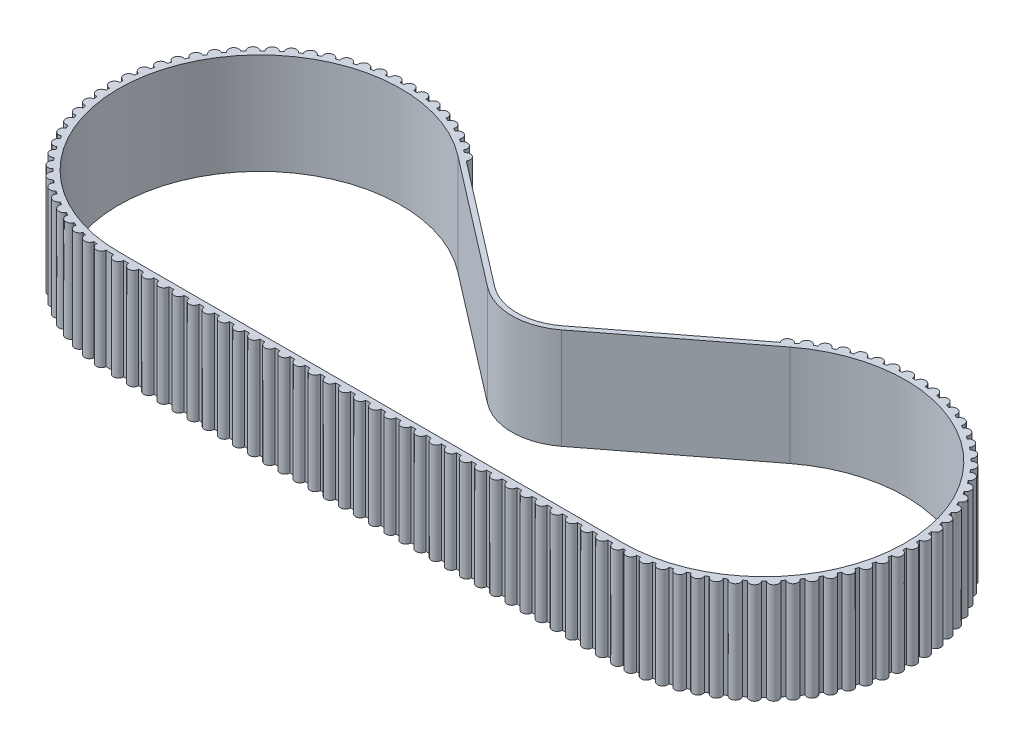
SolidWorks part; units mm, degrees
ref_plane "Front Plane" through (0, 0, 0) normal (0, 0, 1) x (1, 0, 0)
ref_plane "Top Plane" through (0, 0, 0) normal (0, 1, 0) x (1, 0, 0)
ref_plane "Right Plane" through (0, 0, 0) normal (1, 0, 0) x (0, 0, -1)
sketch "Sketch1" plane through (0, 0, 0) normal (0, 1, 0) x (1, 0, 0)
  line L0 (0, 0) -> (50, 0) construction
  line L1 (0, 14) -> (50, 14) construction
  line L2 (0, -14) -> (50, -14) construction
  line L3 (0, 14) -> (25, 6) construction
  line L4 (25, 6) -> (50, 14) construction
  line L5 (25, 6) -> (25, 14) construction
  line L6 (28.6587, 1.2446) -> (41.463, 11.096)
  line L7 (21.3413, 1.2446) -> (8.537, 11.096)
  circle A0 centre (0, 0) radius 14 construction
  circle A1 centre (50, 0) radius 14 construction
  circle A2 centre (25, 6) radius 6 construction
  arc A3 (8.537, 11.096) -> (0, -14) centre (0, 0) ccw
  arc A4 (41.463, 11.096) -> (50, -14) centre (50, 0) cw
  arc A5 (21.3413, 1.2446) -> (28.6587, 1.2446) centre (25, 6) ccw
  dimension "D1" = 28
  dimension "D2" = 12
  dimension "D3" = 50
  dimension "D4" = 8
sketch "Sketch2" plane through (0, 0, 0) normal (0, 1, 0) x (1, 0, 0)
  line L0 (1, -14.5) -> (1.5, -14.5)
  line L1 (49, -14.5) -> (49.5, -14.5)
  line L2 (28.6587, 1.2446) -> (41.463, 11.096)
  line L3 (21.3413, 1.2446) -> (8.537, 11.096)
  line L4 (47.5, -14.5) -> (48, -14.5)
  line L5 (21.6462, 1.6409) -> (8.8419, 11.4922) construction
  line L6 (28.3538, 1.6409) -> (41.1581, 11.4922) construction
  line L7 (46, -14.5) -> (46.5, -14.5)
  line L8 (44.5, -14.5) -> (45, -14.5)
  line L9 (43, -14.5) -> (43.5, -14.5)
  line L10 (41.5, -14.5) -> (42, -14.5)
  line L11 (40, -14.5) -> (40.5, -14.5)
  line L12 (38.5, -14.5) -> (39, -14.5)
  line L13 (37, -14.5) -> (37.5, -14.5)
  line L14 (35.5, -14.5) -> (36, -14.5)
  line L15 (34, -14.5) -> (34.5, -14.5)
  line L16 (32.5, -14.5) -> (33, -14.5)
  line L17 (31, -14.5) -> (31.5, -14.5)
  line L18 (29.5, -14.5) -> (30, -14.5)
  line L19 (28, -14.5) -> (28.5, -14.5)
  line L20 (26.5, -14.5) -> (27, -14.5)
  line L21 (25, -14.5) -> (25.5, -14.5)
  line L22 (23.5, -14.5) -> (24, -14.5)
  line L23 (22, -14.5) -> (22.5, -14.5)
  line L24 (20.5, -14.5) -> (21, -14.5)
  line L25 (19, -14.5) -> (19.5, -14.5)
  line L26 (17.5, -14.5) -> (18, -14.5)
  line L27 (16, -14.5) -> (16.5, -14.5)
  line L28 (14.5, -14.5) -> (15, -14.5)
  line L29 (13, -14.5) -> (13.5, -14.5)
  line L30 (11.5, -14.5) -> (12, -14.5)
  line L31 (10, -14.5) -> (10.5, -14.5)
  line L32 (8.5, -14.5) -> (9, -14.5)
  line L33 (7, -14.5) -> (7.5, -14.5)
  line L34 (5.5, -14.5) -> (6, -14.5)
  line L35 (4, -14.5) -> (4.5, -14.5)
  line L36 (2.5, -14.5) -> (3, -14.5)
  line L37 (25, 6) -> (25, 14) construction
  line L38 (0, 14) -> (50, 14) construction
  line L39 (9.4327, 11.0377) -> (21.6462, 1.6409)
  line L40 (40.5792, 11.0227) -> (28.3538, 1.6409)
  line L41 (0, -14) -> (50, -14)
  line L45 (0, -14) -> (50, -14) construction
  line L47 (0, -14.5) -> (50, -14.5) construction
  arc A0 (0, -14.5) -> (1, -14.5) centre (0.5, -14.5) ccw
  arc A1 (0, -14) -> (8.537, 11.096) centre (0, 0) cw
  arc A2 (8.537, 11.096) -> (0, -14) centre (0, 0) ccw construction
  arc A3 (21.3413, 1.2446) -> (28.6587, 1.2446) centre (25, 6) ccw
  arc A4 (21.3413, 1.2446) -> (28.6587, 1.2446) centre (25, 6) ccw construction
  arc A5 (41.463, 11.096) -> (50, -14) centre (50, 0) cw
  arc A6 (50, -14) -> (41.463, 11.096) centre (50, 0) ccw construction
  arc A7 (0, -14.5) -> (8.8419, 11.4922) centre (0, 0) cw construction
  arc A8 (21.6462, 1.6409) -> (28.3538, 1.6409) centre (25, 6) ccw
  arc A9 (41.3612, 11.6457) -> (41.6459, 11.8515) centre (50, 0) cw
  arc A10 (1.5, -14.5) -> (2.5, -14.5) centre (2, -14.5) ccw
  arc A11 (3, -14.5) -> (4, -14.5) centre (3.5, -14.5) ccw
  arc A12 (4.5, -14.5) -> (5.5, -14.5) centre (5, -14.5) ccw
  arc A13 (6, -14.5) -> (7, -14.5) centre (6.5, -14.5) ccw
  arc A14 (7.5, -14.5) -> (8.5, -14.5) centre (8, -14.5) ccw
  arc A15 (9, -14.5) -> (10, -14.5) centre (9.5, -14.5) ccw
  arc A16 (10.5, -14.5) -> (11.5, -14.5) centre (11, -14.5) ccw
  arc A17 (12, -14.5) -> (13, -14.5) centre (12.5, -14.5) ccw
  arc A18 (13.5, -14.5) -> (14.5, -14.5) centre (14, -14.5) ccw
  arc A19 (15, -14.5) -> (16, -14.5) centre (15.5, -14.5) ccw
  arc A20 (16.5, -14.5) -> (17.5, -14.5) centre (17, -14.5) ccw
  arc A21 (18, -14.5) -> (19, -14.5) centre (18.5, -14.5) ccw
  arc A22 (19.5, -14.5) -> (20.5, -14.5) centre (20, -14.5) ccw
  arc A23 (21, -14.5) -> (22, -14.5) centre (21.5, -14.5) ccw
  arc A24 (22.5, -14.5) -> (23.5, -14.5) centre (23, -14.5) ccw
  arc A25 (24, -14.5) -> (25, -14.5) centre (24.5, -14.5) ccw
  arc A26 (25.5, -14.5) -> (26.5, -14.5) centre (26, -14.5) ccw
  arc A27 (27, -14.5) -> (28, -14.5) centre (27.5, -14.5) ccw
  arc A28 (28.5, -14.5) -> (29.5, -14.5) centre (29, -14.5) ccw
  arc A29 (30, -14.5) -> (31, -14.5) centre (30.5, -14.5) ccw
  arc A30 (31.5, -14.5) -> (32.5, -14.5) centre (32, -14.5) ccw
  arc A31 (33, -14.5) -> (34, -14.5) centre (33.5, -14.5) ccw
  arc A32 (34.5, -14.5) -> (35.5, -14.5) centre (35, -14.5) ccw
  arc A33 (36, -14.5) -> (37, -14.5) centre (36.5, -14.5) ccw
  arc A34 (37.5, -14.5) -> (38.5, -14.5) centre (38, -14.5) ccw
  arc A35 (39, -14.5) -> (40, -14.5) centre (39.5, -14.5) ccw
  arc A36 (40.5, -14.5) -> (41.5, -14.5) centre (41, -14.5) ccw
  arc A37 (42, -14.5) -> (43, -14.5) centre (42.5, -14.5) ccw
  arc A38 (43.5, -14.5) -> (44.5, -14.5) centre (44, -14.5) ccw
  arc A39 (45, -14.5) -> (46, -14.5) centre (45.5, -14.5) ccw
  arc A40 (46.5, -14.5) -> (47.5, -14.5) centre (47, -14.5) ccw
  arc A41 (48, -14.5) -> (49, -14.5) centre (48.5, -14.5) ccw
  arc A42 (49.5, -14.5) -> (50.4999, -14.4914) centre (50, -14.5) ccw
  arc A43 (50.753, -14.4804) -> (51.7491, -14.3941) centre (51.2518, -14.4459) ccw
  arc A44 (52.0973, -14.3475) -> (53.081, -14.1689) centre (52.5907, -14.2667) ccw
  arc A45 (53.4234, -14.0901) -> (54.3862, -13.8207) centre (53.9071, -13.9637) ccw
  arc A46 (54.7198, -13.7104) -> (55.6534, -13.3525) centre (55.1897, -13.5395) ccw
  arc A47 (55.9752, -13.2116) -> (56.8715, -12.7684) centre (56.4271, -12.9978) ccw
  arc A48 (57.1788, -12.5982) -> (58.0299, -12.0736) centre (57.6089, -12.3432) ccw
  arc A49 (58.32, -11.8755) -> (59.1186, -11.2739) centre (58.7245, -11.5816) ccw
  arc A50 (59.3891, -11.0497) -> (60.1282, -10.3764) centre (59.7645, -10.7194) ccw
  arc A51 (60.3766, -10.128) -> (61.0499, -9.3888) centre (60.7197, -9.7642) ccw
  arc A52 (61.2741, -9.1183) -> (61.8757, -8.3197) centre (61.5818, -8.7242) ccw
  arc A53 (62.0738, -8.0296) -> (62.5984, -7.1784) centre (62.3434, -7.6085) ccw
  arc A54 (62.7686, -6.8711) -> (63.2118, -5.9748) centre (62.9979, -6.4268) ccw
  arc A55 (63.3527, -5.653) -> (63.7105, -4.7194) centre (63.5396, -5.1893) ccw
  arc A56 (63.8208, -4.3859) -> (64.0902, -3.423) centre (63.9638, -3.9067) ccw
  arc A57 (64.169, -3.0806) -> (64.3476, -2.0969) centre (64.2668, -2.5903) ccw
  arc A58 (64.3942, -1.7487) -> (64.4805, -0.7526) centre (64.4459, -1.2514) ccw
  arc A59 (64.4944, -0.4015) -> (64.4877, 0.5983) centre (64.4997, 0.0984) ccw
  arc A60 (64.4689, 0.9491) -> (64.3691, 1.9439) centre (64.4276, 1.4474) ccw
  arc A61 (64.3178, 2.2915) -> (64.1258, 3.2727) centre (64.2303, 2.7838) ccw
  arc A62 (64.0424, 3.614) -> (63.76, 4.5731) centre (63.9095, 4.096) ccw
  arc A63 (63.6451, 4.9051) -> (63.2747, 5.8338) centre (63.4679, 5.3726) ccw
  arc A64 (63.1295, 6.1537) -> (62.6742, 7.0438) centre (62.9095, 6.6027) ccw
  arc A65 (62.4998, 7.3488) -> (61.9636, 8.1927) centre (62.239, 7.7754) ccw
  arc A66 (61.7617, 8.4802) -> (61.1493, 9.2706) centre (61.4623, 8.8806) ccw
  arc A67 (60.9214, 9.5379) -> (60.2382, 10.2679) centre (60.5861, 9.9088) ccw
  arc A68 (59.9864, 10.5129) -> (59.2382, 11.1761) centre (59.618, 10.851) ccw
  arc A69 (58.9647, 11.3966) -> (58.158, 11.9873) centre (58.5665, 11.699) ccw
  arc A70 (57.8652, 12.1815) -> (57.0071, 12.6945) centre (57.4406, 12.4454) ccw
  arc A71 (56.6975, 12.8606) -> (55.7953, 13.2915) centre (56.2501, 13.0838) ccw
  arc A72 (55.4716, 13.428) -> (54.5332, 13.7732) centre (55.0054, 13.6087) ccw
  arc A73 (54.1982, 13.8789) -> (53.2318, 14.1353) centre (53.7172, 14.0154) ccw
  arc A74 (52.8884, 14.2094) -> (51.9023, 14.3747) centre (52.3968, 14.3005) ccw
  arc A75 (51.5535, 14.4165) -> (50.5563, 14.4893) centre (51.0555, 14.4615) ccw
  arc A76 (50.2051, 14.4985) -> (49.2055, 14.4782) centre (49.7051, 14.497) ccw
  arc A77 (48.855, 14.4547) -> (47.8615, 14.3414) centre (48.3573, 14.4066) ccw
  arc A78 (47.5147, 14.2854) -> (46.5362, 14.0802) centre (47.0237, 14.1913) ccw
  arc A79 (46.1961, 13.9922) -> (45.2409, 13.6967) centre (45.7159, 13.8527) ccw
  arc A80 (44.9105, 13.5774) -> (43.9869, 13.1944) centre (44.4454, 13.3939) ccw
  arc A81 (43.669, 13.0449) -> (42.7851, 12.5776) centre (43.223, 12.8188) ccw
  arc A82 (42.4825, 12.3991) -> (41.6459, 11.8515) centre (42.0595, 12.1325) ccw
  arc A83 (41.3612, 11.6457) -> (40.5792, 11.0227) centre (40.9649, 11.3409) ccw
  arc A84 (50.753, -14.4804) -> (50.4999, -14.4914) centre (50, 0) cw
  arc A85 (52.0973, -14.3475) -> (51.7491, -14.3941) centre (50, 0) cw
  arc A86 (41.1581, 11.4922) -> (50, -14.5) centre (50, 0) cw construction
  arc A87 (53.4234, -14.0901) -> (53.081, -14.1689) centre (50, 0) cw
  arc A88 (54.7198, -13.7104) -> (54.3862, -13.8207) centre (50, 0) cw
  arc A89 (55.9752, -13.2116) -> (55.6534, -13.3525) centre (50, 0) cw
  arc A90 (57.1788, -12.5982) -> (56.8715, -12.7684) centre (50, 0) cw
  arc A91 (58.32, -11.8755) -> (58.0299, -12.0736) centre (50, 0) cw
  arc A92 (60.3766, -10.128) -> (60.1282, -10.3764) centre (50, 0) cw
  arc A93 (59.3891, -11.0497) -> (59.1186, -11.2739) centre (50, 0) cw
  arc A94 (61.2741, -9.1183) -> (61.0499, -9.3888) centre (50, 0) cw
  arc A95 (62.0738, -8.0296) -> (61.8757, -8.3197) centre (50, 0) cw
  arc A96 (62.7686, -6.8711) -> (62.5984, -7.1784) centre (50, 0) cw
  arc A97 (63.3527, -5.653) -> (63.2118, -5.9748) centre (50, 0) cw
  arc A98 (64.169, -3.0806) -> (64.0902, -3.423) centre (50, 0) cw
  arc A99 (64.3942, -1.7487) -> (64.3476, -2.0969) centre (50, 0) cw
  arc A100 (64.4944, -0.4015) -> (64.4805, -0.7526) centre (50, 0) cw
  arc A101 (64.4689, 0.9491) -> (64.4877, 0.5983) centre (50, 0) cw
  arc A102 (64.3178, 2.2915) -> (64.3691, 1.9439) centre (50, 0) cw
  arc A103 (64.0424, 3.614) -> (64.1258, 3.2727) centre (50, 0) cw
  arc A104 (63.6451, 4.9051) -> (63.76, 4.5731) centre (50, 0) cw
  arc A105 (63.1295, 6.1537) -> (63.2747, 5.8338) centre (50, 0) cw
  arc A106 (62.4998, 7.3488) -> (62.6742, 7.0438) centre (50, 0) cw
  arc A107 (61.7617, 8.4802) -> (61.9636, 8.1927) centre (50, 0) cw
  arc A108 (60.9214, 9.5379) -> (61.1493, 9.2706) centre (50, 0) cw
  arc A109 (59.9864, 10.5129) -> (60.2382, 10.2679) centre (50, 0) cw
  arc A110 (58.9647, 11.3966) -> (59.2382, 11.1761) centre (50, 0) cw
  arc A111 (57.8652, 12.1815) -> (58.158, 11.9873) centre (50, 0) cw
  arc A112 (56.6975, 12.8606) -> (57.0071, 12.6945) centre (50, 0) cw
  arc A113 (55.4716, 13.428) -> (55.7953, 13.2915) centre (50, 0) cw
  arc A114 (54.1982, 13.8789) -> (54.5332, 13.7732) centre (50, 0) cw
  arc A115 (52.8884, 14.2094) -> (53.2318, 14.1353) centre (50, 0) cw
  arc A116 (51.5535, 14.4165) -> (51.9023, 14.3747) centre (50, 0) cw
  arc A117 (50.2051, 14.4985) -> (50.5563, 14.4893) centre (50, 0) cw
  arc A118 (47.5147, 14.2854) -> (47.8615, 14.3414) centre (50, 0) cw
  arc A119 (48.855, 14.4547) -> (49.2055, 14.4782) centre (50, 0) cw
  arc A120 (46.1961, 13.9922) -> (46.5362, 14.0802) centre (50, 0) cw
  arc A121 (44.9105, 13.5774) -> (45.2409, 13.6967) centre (50, 0) cw
  arc A122 (43.669, 13.0449) -> (43.9869, 13.1944) centre (50, 0) cw
  arc A123 (42.4825, 12.3991) -> (42.7851, 12.5776) centre (50, 0) cw
  arc A124 (63.8208, -4.3859) -> (63.7105, -4.7194) centre (50, 0) cw
  arc A125 (-3.081, -14.1689) -> (-2.0973, -14.3475) centre (-2.5907, -14.2667) ccw
  arc A126 (-13.8208, -4.3859) -> (-13.7105, -4.7194) centre (0, 0) ccw
  arc A127 (-2.0973, -14.3475) -> (-1.7491, -14.3941) centre (0, 0) ccw
  arc A148 (-0.753, -14.4804) -> (0, -14.5) centre (0, 0) ccw
  arc A149 (-0.753, -14.4804) -> (-1.7491, -14.3941) centre (-1.2518, -14.4459) cw
  arc A150 (-3.4234, -14.0901) -> (-3.081, -14.1689) centre (0, 0) ccw
  arc A151 (-3.4234, -14.0901) -> (-4.3862, -13.8207) centre (-3.9071, -13.9637) cw
  arc A152 (-4.7198, -13.7104) -> (-4.3862, -13.8207) centre (0, 0) ccw
  arc A153 (-4.7198, -13.7104) -> (-5.6534, -13.3525) centre (-5.1897, -13.5395) cw
  arc A154 (7.5175, 12.3991) -> (7.2149, 12.5776) centre (0, 0) ccw
  arc A155 (6.331, 13.0449) -> (6.0131, 13.1944) centre (0, 0) ccw
  arc A156 (5.0895, 13.5774) -> (4.7591, 13.6967) centre (0, 0) ccw
  arc A157 (3.8039, 13.9922) -> (3.4638, 14.0802) centre (0, 0) ccw
  arc A158 (1.145, 14.4547) -> (0.7945, 14.4782) centre (0, 0) ccw
  arc A159 (2.4853, 14.2854) -> (2.1385, 14.3414) centre (0, 0) ccw
  arc A160 (-0.2051, 14.4985) -> (-0.5563, 14.4893) centre (0, 0) ccw
  arc A161 (-1.5535, 14.4165) -> (-1.9023, 14.3747) centre (0, 0) ccw
  arc A162 (-2.8884, 14.2094) -> (-3.2318, 14.1353) centre (0, 0) ccw
  arc A163 (-4.1982, 13.8789) -> (-4.5332, 13.7732) centre (0, 0) ccw
  arc A164 (-5.4716, 13.428) -> (-5.7953, 13.2915) centre (0, 0) ccw
  arc A165 (-6.6975, 12.8606) -> (-7.0071, 12.6945) centre (0, 0) ccw
  arc A166 (-7.8652, 12.1815) -> (-8.158, 11.9873) centre (0, 0) ccw
  arc A167 (-8.9647, 11.3966) -> (-9.2382, 11.1761) centre (0, 0) ccw
  arc A168 (-9.9864, 10.5129) -> (-10.2382, 10.2679) centre (0, 0) ccw
  arc A169 (-10.9214, 9.5379) -> (-11.1493, 9.2706) centre (0, 0) ccw
  arc A170 (-11.7617, 8.4802) -> (-11.9636, 8.1927) centre (0, 0) ccw
  arc A171 (-12.4998, 7.3488) -> (-12.6742, 7.0438) centre (0, 0) ccw
  arc A172 (-13.1295, 6.1537) -> (-13.2747, 5.8338) centre (0, 0) ccw
  arc A173 (-13.6451, 4.9051) -> (-13.76, 4.5731) centre (0, 0) ccw
  arc A174 (-14.0424, 3.614) -> (-14.1258, 3.2727) centre (0, 0) ccw
  arc A175 (-14.3178, 2.2915) -> (-14.3691, 1.9439) centre (0, 0) ccw
  arc A176 (-14.4689, 0.9491) -> (-14.4877, 0.5983) centre (0, 0) ccw
  arc A177 (-14.4944, -0.4015) -> (-14.4805, -0.7526) centre (0, 0) ccw
  arc A178 (-14.3942, -1.7487) -> (-14.3476, -2.0969) centre (0, 0) ccw
  arc A179 (-14.169, -3.0806) -> (-14.0902, -3.423) centre (0, 0) ccw
  arc A180 (-13.3527, -5.653) -> (-13.2118, -5.9748) centre (0, 0) ccw
  arc A181 (-12.7686, -6.8711) -> (-12.5984, -7.1784) centre (0, 0) ccw
  arc A182 (-12.0738, -8.0296) -> (-11.8757, -8.3197) centre (0, 0) ccw
  arc A183 (-11.2741, -9.1183) -> (-11.0499, -9.3888) centre (0, 0) ccw
  arc A184 (-9.3891, -11.0497) -> (-9.1186, -11.2739) centre (0, 0) ccw
  arc A185 (-10.3766, -10.128) -> (-10.1282, -10.3764) centre (0, 0) ccw
  arc A186 (-8.32, -11.8755) -> (-8.0299, -12.0736) centre (0, 0) ccw
  arc A187 (-7.1788, -12.5982) -> (-6.8715, -12.7684) centre (0, 0) ccw
  arc A188 (-5.9752, -13.2116) -> (-5.6534, -13.3525) centre (0, 0) ccw
  arc A189 (8.6388, 11.6457) -> (9.4327, 11.0377) centre (9.0351, 11.3409) cw
  arc A190 (7.5175, 12.3991) -> (8.3541, 11.8515) centre (7.9405, 12.1325) cw
  arc A191 (6.331, 13.0449) -> (7.2149, 12.5776) centre (6.777, 12.8188) cw
  arc A192 (5.0895, 13.5774) -> (6.0131, 13.1944) centre (5.5546, 13.3939) cw
  arc A193 (3.8039, 13.9922) -> (4.7591, 13.6967) centre (4.2841, 13.8527) cw
  arc A194 (2.4853, 14.2854) -> (3.4638, 14.0802) centre (2.9763, 14.1913) cw
  arc A195 (1.145, 14.4547) -> (2.1385, 14.3414) centre (1.6427, 14.4066) cw
  arc A196 (-0.2051, 14.4985) -> (0.7945, 14.4782) centre (0.2949, 14.497) cw
  arc A197 (-1.5535, 14.4165) -> (-0.5563, 14.4893) centre (-1.0555, 14.4615) cw
  arc A198 (-2.8884, 14.2094) -> (-1.9023, 14.3747) centre (-2.3968, 14.3005) cw
  arc A199 (-4.1982, 13.8789) -> (-3.2318, 14.1353) centre (-3.7172, 14.0154) cw
  arc A200 (-5.4716, 13.428) -> (-4.5332, 13.7732) centre (-5.0054, 13.6087) cw
  arc A201 (-6.6975, 12.8606) -> (-5.7953, 13.2915) centre (-6.2501, 13.0838) cw
  arc A202 (-7.8652, 12.1815) -> (-7.0071, 12.6945) centre (-7.4406, 12.4454) cw
  arc A203 (-8.9647, 11.3966) -> (-8.158, 11.9873) centre (-8.5665, 11.699) cw
  arc A204 (-9.9864, 10.5129) -> (-9.2382, 11.1761) centre (-9.618, 10.851) cw
  arc A205 (-10.9214, 9.5379) -> (-10.2382, 10.2679) centre (-10.5861, 9.9088) cw
  arc A206 (-11.7617, 8.4802) -> (-11.1493, 9.2706) centre (-11.4623, 8.8806) cw
  arc A207 (-12.4998, 7.3488) -> (-11.9636, 8.1927) centre (-12.239, 7.7754) cw
  arc A208 (-13.1295, 6.1537) -> (-12.6742, 7.0438) centre (-12.9095, 6.6027) cw
  arc A209 (-13.6451, 4.9051) -> (-13.2747, 5.8338) centre (-13.4679, 5.3726) cw
  arc A210 (-14.0424, 3.614) -> (-13.76, 4.5731) centre (-13.9095, 4.096) cw
  arc A211 (-14.3178, 2.2915) -> (-14.1258, 3.2727) centre (-14.2303, 2.7838) cw
  arc A212 (-14.4689, 0.9491) -> (-14.3691, 1.9439) centre (-14.4276, 1.4474) cw
  arc A213 (-14.4944, -0.4015) -> (-14.4877, 0.5983) centre (-14.4997, 0.0984) cw
  arc A214 (-14.3942, -1.7487) -> (-14.4805, -0.7526) centre (-14.4459, -1.2514) cw
  arc A215 (-14.169, -3.0806) -> (-14.3476, -2.0969) centre (-14.2668, -2.5903) cw
  arc A216 (-13.8208, -4.3859) -> (-14.0902, -3.423) centre (-13.9638, -3.9067) cw
  arc A217 (-13.3527, -5.653) -> (-13.7105, -4.7194) centre (-13.5396, -5.1893) cw
  arc A218 (-12.7686, -6.8711) -> (-13.2118, -5.9748) centre (-12.9979, -6.4268) cw
  arc A219 (-12.0738, -8.0296) -> (-12.5984, -7.1784) centre (-12.3434, -7.6085) cw
  arc A220 (-11.2741, -9.1183) -> (-11.8757, -8.3197) centre (-11.5818, -8.7242) cw
  arc A221 (-10.3766, -10.128) -> (-11.0499, -9.3888) centre (-10.7197, -9.7642) cw
  arc A222 (-9.3891, -11.0497) -> (-10.1282, -10.3764) centre (-9.7645, -10.7194) cw
  arc A223 (-8.32, -11.8755) -> (-9.1186, -11.2739) centre (-8.7245, -11.5816) cw
  arc A224 (-7.1788, -12.5982) -> (-8.0299, -12.0736) centre (-7.6089, -12.3432) cw
  arc A225 (8.6388, 11.6457) -> (8.3541, 11.8515) centre (0, 0) ccw
  arc A227 (-6.8715, -12.7684) -> (-5.9752, -13.2116) centre (-6.4271, -12.9978) ccw
  point P267 (50, 0)
  dimension "D1" = 1
  dimension "D6" = 1
  dimension "D2" = 0.5
  dimension "D3" = 0.5
  dimension "D4" = 0.5
  dimension "D5" = 34
  dimension "D7" = 41
extrude "Boss-Extrude1" add sketch "Sketch2" along normal blind 10 contours A187 A227 A188 A153 A152 A151 A150 A149 A148 A0 L0 A10 L36 A11 L35 A12 L34 A13 L33 A14 L32 A15 L31 A16 L30 A17 L29 A18 L28 A19 L27 A20 L26 A21 L25 A22 L24 A23 L23 A24 L22 A25 L21 A26 L20 A27 L19 A28 L18
